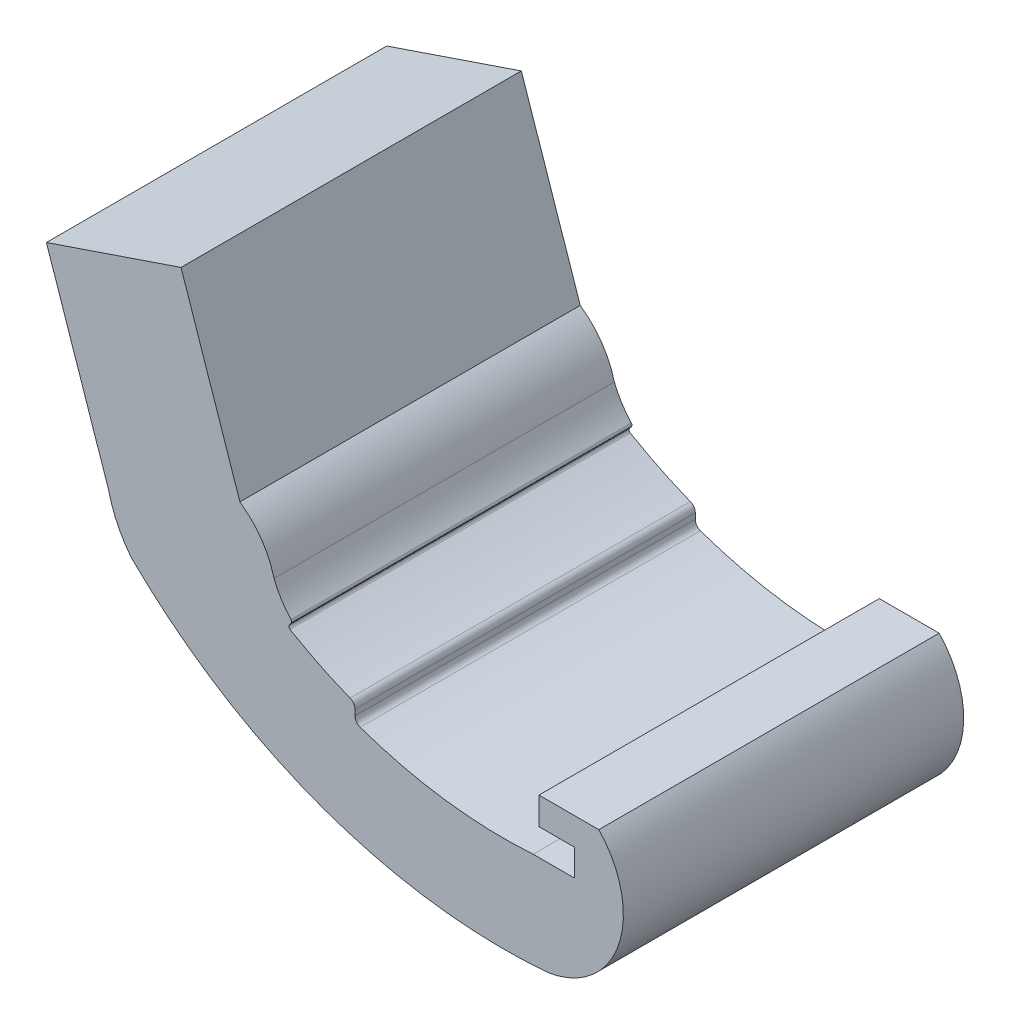
SolidWorks part; units mm, degrees
ref_plane "Front Plane" through (0, 0, 0) normal (0, 0, 1) x (1, 0, 0)
ref_plane "Top Plane" through (0, 0, 0) normal (0, 1, 0) x (1, 0, 0)
ref_plane "Right Plane" through (0, 0, 0) normal (1, 0, 0) x (0, 0, -1)
sketch "Sketch1" plane through (0, 0, 0) normal (0, 0, 1) x (1, 0, 0)
  line L12 (17.1656, -15.1467) -> (19.2502, -15.1467)
  line L13 (19.2756, -15.1213) -> (19.2756, -13.7719)
  line L23 (17.4624, -13.7719) -> (17.4624, -12.3686)
  line L24 (19.2756, -13.7719) -> (17.4624, -13.7719)
  line L27 (8.0214, -13.5698) -> (8.0214, -13.2744)
  line L34 (-5.5185, -9.3147) -> (3.175, -6.3581) construction
  line L35 (3.175, -7.6079) -> (3.175, -6.3581) construction
  line L36 (16.6687, -11.563) -> (20.0821, -11.6137) construction
  line L37 (16.6687, -14.3802) -> (16.6687, -11.563) construction
  line L39 (-4.6205, -9.8477) -> (2.3812, -7.4665) construction
  line L40 (2.3813, -7.584) -> (2.3812, -7.4665) construction
  line L49 (-5.078, -9.5841) -> (2.1567, -7.1236) construction
  line L50 (17.0656, -11.9658) -> (20.0595, -12.0103) construction
  line L51 (17.0656, -14.1688) -> (17.0656, -11.9658) construction
  line L52 (18.8787, -14.1688) -> (17.0656, -14.1688) construction
  line L53 (18.8787, -14.7498) -> (18.8787, -14.1688) construction
  line L54 (17.1521, -14.7498) -> (18.8787, -14.7498) construction
  line L55 (8.4183, -13.5698) -> (8.4183, -13.2744) construction
  line L56 (16.6687, -14.3802) -> (16.6687, -14.3802) construction
  line L57 (16.6687, -14.3802) -> (16.6687, -14.3802) construction
  line L58 (16.6687, -14.3802) -> (16.6687, -14.3802) construction
  line L59 (4.7421, -11.0922) -> (4.6517, -11.2065)
  line L63 (-4.6205, -9.8477) -> (2.2845, -7.4994) construction
  line L64 (2.8383, -7.5479) -> (2.4819, -7.4844) construction
  line L65 (2.9079, -7.1572) -> (2.5515, -7.0937) construction
  line L67 (2.1186, -7.0117) -> (-0.904, 1.8962)
  line L68 (-4.6205, -9.8477) -> (-7.812, -0.4504)
  line L69 (17.4624, -12.3686) -> (20.5352, -12.3686)
  line L71 (-7.812, -0.4504) -> (-0.904, 1.8962)
  line L72 (17.4624, -12.3686) -> (20.0306, -12.4068) construction
  arc A0 (17.1656, -15.1467) -> (8.2871, -13.9444) centre (15.6572, 7.0967) cw
  arc A1 (17.9219, -20.0247) -> (-3.4561, -12.278) centre (15.6572, 7.0967) cw
  arc A2 (-3.4561, -12.278) -> (-4.6205, -9.8477) centre (1.3567, -8.478) cw
  arc A10 (19.2756, -15.1213) -> (19.2502, -15.1467) centre (19.2502, -15.1213) cw
  arc A12 (7.7702, -12.9052) -> (4.6864, -11.3945) centre (15.6572, 7.0967) cw
  arc A18 (-4.0478, -12.8093) -> (-5.5185, -9.3147) centre (1.3567, -8.478) cw construction
  arc A19 (18.1733, -20.7996) -> (-4.0478, -12.8093) centre (15.6572, 7.0967) cw construction
  arc A20 (18.1733, -20.7996) -> (21.0644, -12.7271) centre (14.8303, -15.0483) ccw construction
  arc A21 (20.0821, -11.6137) -> (21.0644, -12.7271) centre (19.9845, -12.6898) cw construction
  arc A22 (16.6687, -14.3802) -> (4.5618, -11.32) centre (15.6572, 7.0967) cw construction
  arc A23 (17.1656, -15.1467) -> (4.0691, -11.9496) centre (15.6572, 7.0967) cw construction
  arc A24 (4.0691, -11.9496) -> (2.3813, -7.584) centre (8.0214, -7.9124) cw construction
  arc A26 (4.5618, -11.32) -> (3.175, -7.6079) centre (8.0214, -7.9124) cw construction
  arc A28 (7.7702, -12.9052) -> (8.0214, -13.2744) centre (7.6246, -13.2744) cw
  arc A29 (8.2871, -13.9444) -> (8.0214, -13.5698) centre (8.4183, -13.5698) cw
  arc A30 (4.7361, -10.9275) -> (3.8702, -9.5405) centre (8.0214, -7.9124) cw
  arc A42 (-3.7522, -12.5434) -> (-5.078, -9.5841) centre (1.3567, -8.478) cw construction
  arc A43 (18.0488, -20.4122) -> (-3.7522, -12.5434) centre (15.6572, 7.0967) cw construction
  arc A44 (18.0488, -20.4122) -> (20.6616, -12.7844) centre (14.8303, -15.0483) ccw construction
  arc A45 (20.0595, -12.0103) -> (20.6616, -12.7844) centre (19.9845, -12.6898) cw construction
  arc A46 (17.1521, -14.7498) -> (8.4183, -13.5698) centre (15.6572, 7.0967) cw construction
  arc A47 (7.9157, -12.536) -> (8.4183, -13.2744) centre (7.6246, -13.2744) cw construction
  arc A48 (7.9157, -12.536) -> (4.8102, -11.0062) centre (15.6572, 7.0967) cw construction
  arc A49 (16.6687, -14.3802) -> (16.6687, -14.3802) centre (16.6687, -14.3802) cw construction
  arc A50 (18.8787, -14.7498) -> (18.8787, -14.7498) centre (18.8787, -14.7498) cw construction
  arc A51 (8.4183, -13.5698) -> (8.4183, -13.5698) centre (8.4183, -13.5698) cw construction
  arc A52 (2.4819, -7.4844) -> (2.2845, -7.4994) centre (2.4123, -7.8751) ccw construction
  arc A53 (3.1655, -7.9367) -> (2.8383, -7.5479) centre (2.7686, -7.9386) ccw construction
  arc A54 (4.5618, -11.32) -> (3.1655, -7.9367) centre (8.0214, -7.9124) cw construction
  arc A55 (2.5515, -7.0937) -> (2.1567, -7.1236) centre (2.4123, -7.8751) ccw construction
  arc A57 (4.8102, -11.0062) -> (3.5624, -7.9347) centre (8.0214, -7.9124) cw construction
  arc A58 (4.7361, -10.9275) -> (4.7421, -11.0922) centre (4.6426, -11.0134) cw
  arc A59 (7.7702, -12.9052) -> (4.5618, -11.32) centre (15.6572, 7.0967) cw construction
  arc A60 (4.6517, -11.2065) -> (4.6864, -11.3945) centre (4.7512, -11.2853) ccw
  arc A64 (3.5624, -7.9347) -> (2.9079, -7.1572) centre (2.7686, -7.9386) ccw construction
  arc A65 (3.8702, -9.5405) -> (2.1186, -7.0117) centre (-0.4002, -10.6273) ccw
  arc A66 (17.9219, -20.0247) -> (20.5352, -12.3686) centre (17.2317, -15.515) ccw
  arc A67 (20.0306, -12.4068) -> (20.2446, -12.8107) centre (19.9845, -12.6898) cw construction
  arc A68 (17.9219, -20.0247) -> (20.2446, -12.8107) centre (14.8303, -15.0483) ccw construction
  dimension "D1" = 1.3494
  dimension "D2" = 0.0254
  dimension "D3" = 0.7937
  dimension "D7" = 0.3969
extrude "Boss-Extrude1" add sketch "Sketch1" along normal blind 17.4625 contours L67 L71 L68 A2 A1 A66 L69 L23 L24 L13 A10 L12 A0 A29 L27 A28 A12 A60 L59 A58 A30 A65
